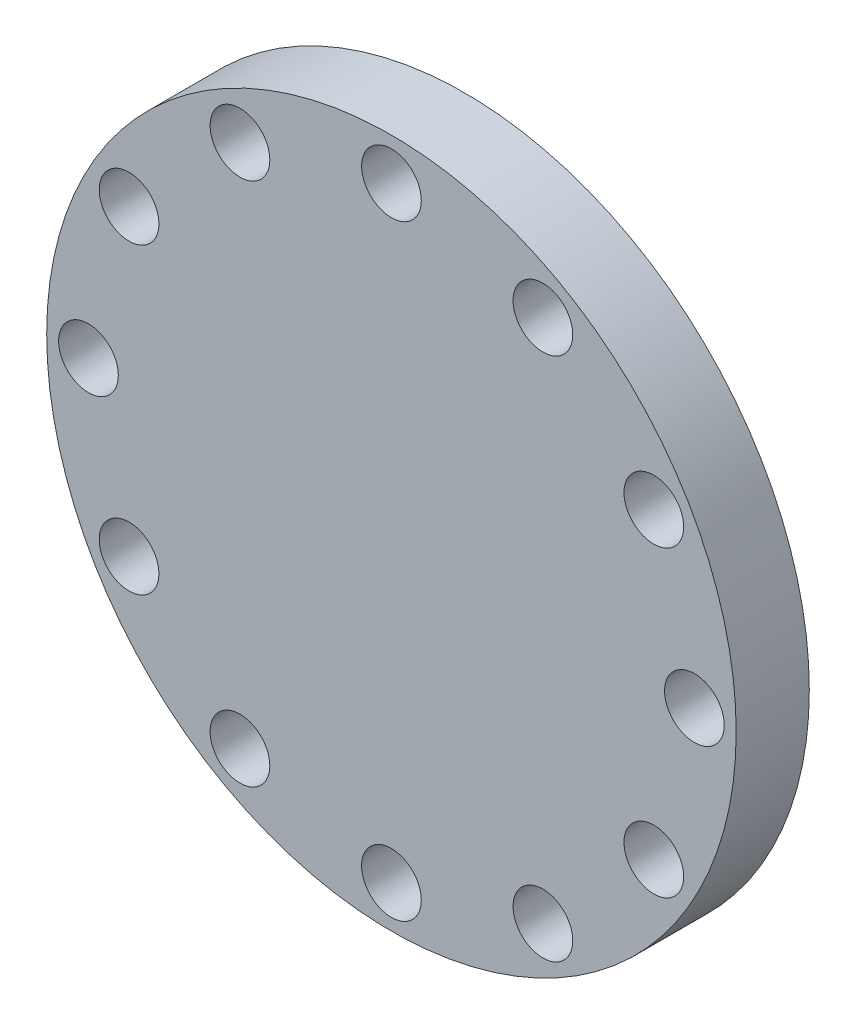
SolidWorks part; units mm, degrees
ref_plane "Front Plane" through (0, 0, 0) normal (0, 0, 1) x (1, 0, 0)
ref_plane "Top Plane" through (0, 0, 0) normal (0, 1, 0) x (1, 0, 0)
ref_plane "Right Plane" through (0, 0, 0) normal (1, 0, 0) x (0, 0, -1)
sketch "Sketch1" plane through (0, 0, 0) normal (0, 0, 1) x (1, 0, 0)
  circle A0 centre (0, 0) radius 330
  circle A1 centre (0, 0) radius 247.5
  dimension "D1" = 660
  dimension "D2" = 495
extrude "Boss-Extrude1" add sketch "Sketch1" along normal blind 70 contours A1 | A0 A1
sketch "Sketch2" plane through (0, 0, 0) normal (0, 0, 1) x (1, 0, 0)
  circle A0 centre (0, 0) radius 290
  circle A1 centre (0, 290) radius 28.575
  circle A2 centre (145, 251.1474) radius 28.575
  circle A3 centre (251.1474, 145) radius 28.575
  circle A4 centre (290, 0) radius 28.575
  circle A5 centre (251.1474, -145) radius 28.575
  circle A6 centre (145, -251.1474) radius 28.575
  circle A7 centre (0, -290) radius 28.575
  circle A8 centre (-145, -251.1474) radius 28.575
  circle A9 centre (-251.1474, -145) radius 28.575
  circle A10 centre (-290, 0) radius 28.575
  circle A11 centre (-251.1474, 145) radius 28.575
  circle A12 centre (-145, 251.1474) radius 28.575
  point P30 (0, 0)
  dimension "D1" = 580
  dimension "D2" = 57.15
  dimension "D3" = 12
extrude "Cut-Extrude1" cut sketch "Sketch2" along normal blind 131 contours A0 A4 | A0 A4 | A0 A6 | A0 A8 | A0 A8 | A5 | A7 | A9 | A10 | A11 | A12 | A1 | A2 | A3
equation "\"2.25inch\"=0.0379964"
